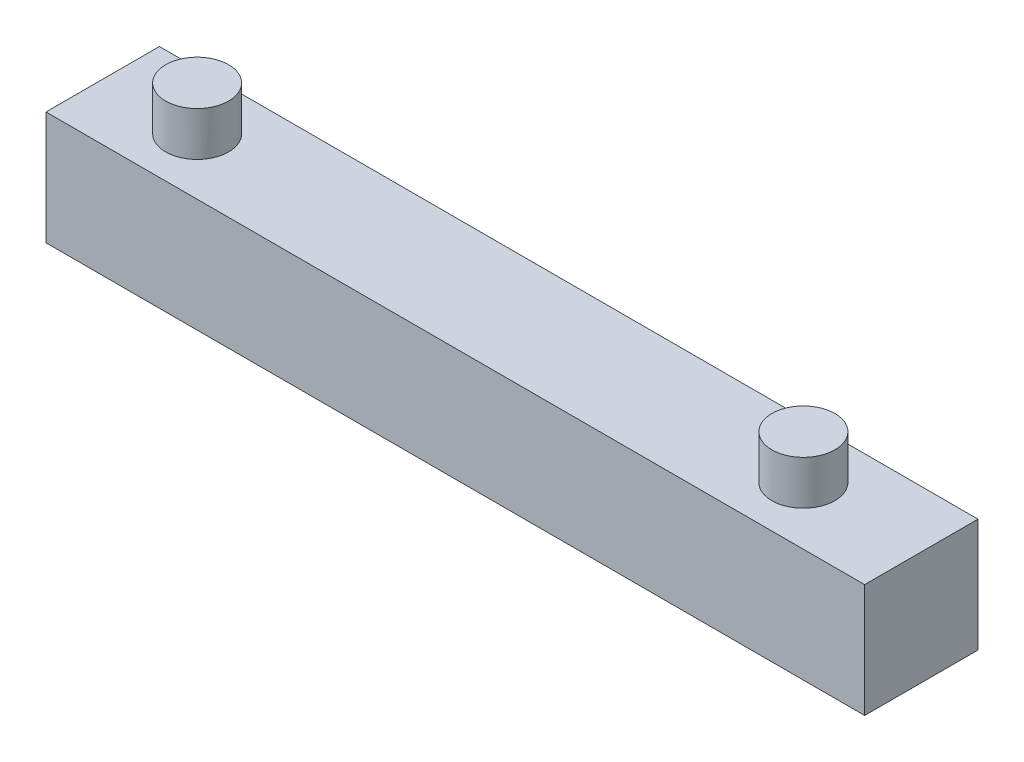
SolidWorks part; units mm, degrees
ref_plane "Front Plane" through (0, 0, 0) normal (0, 0, 1) x (1, 0, 0)
ref_plane "Top Plane" through (0, 0, 0) normal (0, 1, 0) x (1, 0, 0)
ref_plane "Right Plane" through (0, 0, 0) normal (1, 0, 0) x (0, 0, -1)
sketch "Sketch1" plane through (0, 0, 0) normal (0, 0, 1) x (1, 0, 0)
  line L1 (0, 0) -> (65, 0)
  line L2 (0, 0) -> (0, 9)
  line L3 (0, 9) -> (65, 9)
  line L4 (65, 0) -> (65, 9)
  dimension "D1" = 65
  dimension "D2" = 9
extrude "Boss-Extrude1" add sketch "Sketch1" along normal blind 9
sketch "Sketch2" plane through (0, 0, 0) normal (0, 1, 0) x (1, 0, 0)
  line L0 (0, -9) -> (0, 0) construction
  line L1 (65, 0) -> (0, 0) construction
  line L2 (65, -9) -> (65, 0) construction
  circle A0 centre (7.5, -4.5) radius 2.5
  circle A1 centre (57.5, -4.5) radius 2.5
  point P2 (0, -4.5)
  point P9 (65, -4.5)
  dimension "D1" = 5
  dimension "D4" = 5
  dimension "D2" = 7.5
  dimension "D3" = 4.5
  dimension "D5" = 7.5
extrude "Boss-Extrude2" add sketch "Sketch2" along normal blind 3.5
sketch "Sketch3" plane through (0, 9, 0) normal (0, 1, 0) x (1, 0, 0)
  line L0 (0, -9) -> (0, 0) construction
  line L1 (65, 0) -> (0, 0) construction
  circle A0 centre (7.5, -4.5) radius 2.5
  circle A1 centre (55.5492, -4.414) radius 2.5
  point P4 (0, -4.5)
  dimension "D1" = 5
  dimension "D2" = 7.5
  dimension "D3" = 4.5
extrude "Boss-Extrude3" add sketch "Sketch3" along normal blind 3.5
